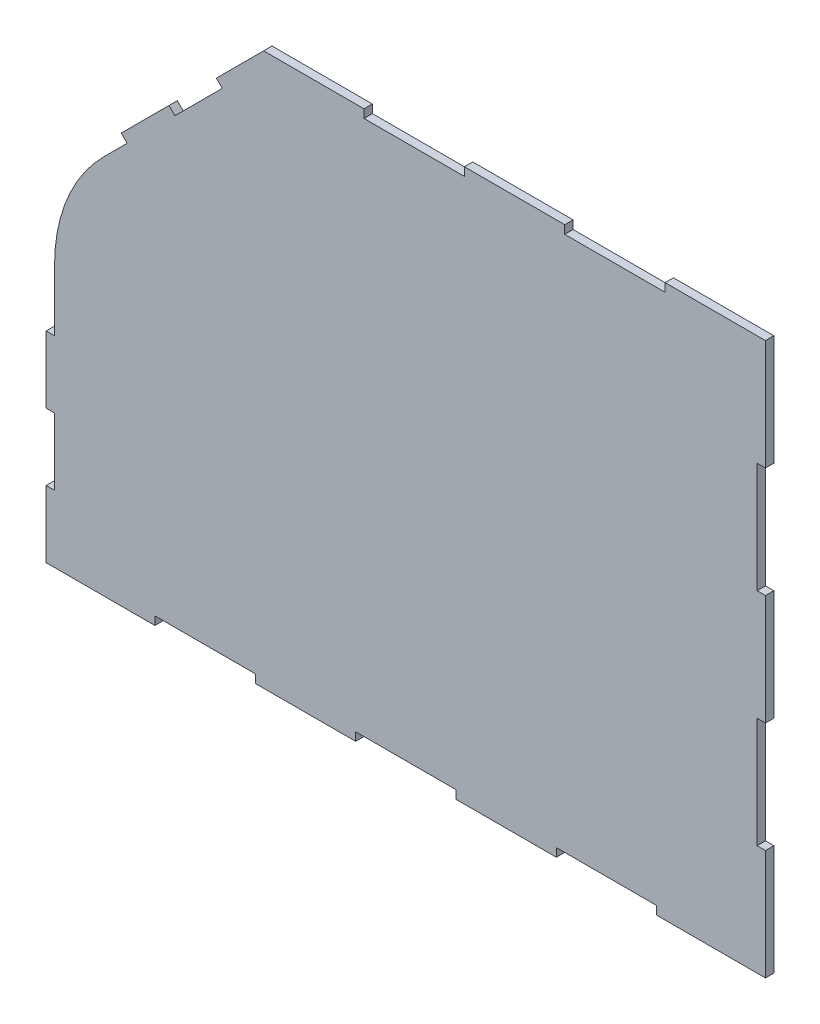
SolidWorks part; units mm, degrees
material "Contreplaqué pin"
ref_plane "Plan de face" through (0, 0, 0) normal (0, 0, 1) x (1, 0, 0)
ref_plane "Plan de dessus" through (0, 0, 0) normal (0, 1, 0) x (1, 0, 0)
ref_plane "Plan de droite" through (0, 0, 0) normal (1, 0, 0) x (0, 0, -1)
sketch "Esquisse1" plane through (0, 0, 0) normal (0, 0, 1) x (1, 0, 0)
  line L1 (0, 330) -> (-60, 330)
  line L2 (-300, 330) -> (-328.2843, 301.7157)
  line L3 (-430, 200) -> (-430, 160)
  line L4 (-305, 0) -> (-245, 0)
  line L5 (-240, 330) -> (-300, 330)
  line L7 (-240, 330) -> (-240, 325)
  line L8 (-240, 325) -> (-180, 325)
  line L9 (-180, 330) -> (-180, 325)
  line L11 (-120, 330) -> (-120, 325)
  line L12 (-120, 325) -> (-60, 325)
  line L13 (-60, 330) -> (-60, 325)
  line L14 (-120, 330) -> (-180, 330)
  line L31 (-328.2843, 301.7157) -> (-324.7487, 298.1802)
  line L32 (-324.7487, 298.1802) -> (-353.033, 269.8959)
  line L33 (-353.033, 269.8959) -> (-356.5685, 273.4315)
  line L34 (-399.9019, 230.0981) -> (-396.3663, 226.5626)
  line L35 (-396.3663, 226.5626) -> (-411.4154, 211.5135)
  line L36 (-411.4154, 211.5135) -> (-414.9509, 215.0491)
  line L37 (-356.5685, 273.4315) -> (-399.9019, 230.0981)
  line L38 (-414.9509, 215.0491) -> (-430, 200)
  line L39 (-430, 120) -> (-430, 80)
  line L44 (-430, 160) -> (-425, 160)
  line L46 (-430, 120) -> (-425, 120)
  line L47 (-425, 160) -> (-425, 120)
  line L48 (-430, 80) -> (-425, 80)
  line L50 (-430, 40) -> (-425, 40)
  line L51 (-425, 80) -> (-425, 40)
  line L52 (-430, 40) -> (-430, 0)
  line L53 (0, 0) -> (0, 66)
  line L54 (0, 66) -> (-5, 66)
  line L55 (-5, 66) -> (-5, 132)
  line L56 (-5, 132) -> (0, 132)
  line L57 (0, 132) -> (0, 198)
  line L58 (0, 198) -> (-5, 198)
  line L59 (-5, 198) -> (-5, 264)
  line L60 (-5, 264) -> (0, 264)
  line L61 (0, 264) -> (0, 330)
  line L62 (-384.8528, 245.1472) -> (-351.7904, 212.0848) construction
  line L63 (-365, 0) -> (-365, 5)
  line L64 (-365, 5) -> (-305, 5)
  line L65 (-305, 5) -> (-305, 0)
  line L66 (-305, 0) -> (-245, 0)
  line L67 (-245, 0) -> (-245, 5)
  line L68 (-245, 5) -> (-185, 5)
  line L69 (-185, 5) -> (-185, 0)
  line L70 (-185, 0) -> (-125, 0)
  line L71 (-125, 0) -> (-125, 5)
  line L72 (-125, 5) -> (-65, 5)
  line L73 (-65, 5) -> (-65, 0)
  line L74 (-65, 0) -> (0, 0)
  line L75 (-430, 0) -> (-365, 0)
  line L76 (-185, 0) -> (-125, 0)
  line L77 (-65, 0) -> (0, 0)
  point P42 (-430, 180)
  dimension "D1" = 200
  dimension "D2" = 330
  dimension "D3" = 300
  dimension "D5" = 5
  dimension "D8" = 5
  dimension "D9" = 5
  dimension "D4" = 430
  dimension "D6" = 5
  dimension "D7" = 120
  dimension "D10" = 63.8478
  dimension "D11" = 40
  dimension "D12" = 40
  dimension "D13" = 21.2826
  dimension "D14" = 21.2826
  dimension "D15" = 65
  dimension "D16" = 65
  dimension "D17" = 60
  dimension "D18" = 5
extrude "Boss.-Extru.1" add sketch "Esquisse1" along normal blind 5
sketch "Esquisse2" plane through (0, 0, 5) normal (0, 0, 1) x (1, 0, 0)
  line L0 (-395.7107, 227.2183) -> (-381.5685, 241.3604)
  line L1 (-381.5685, 241.3604) -> (-385.1041, 244.8959)
  line L2 (-425, 156.5076) -> (-430, 156.5076)
  line L3 (-430, 156.5076) -> (-430, 200)
  line L4 (-430, 200) -> (-385.1041, 244.8959)
  line L5 (-356.5685, 273.4315) -> (-399.9019, 230.0981) construction
  line L9 (-430, 120) -> (-430, 80) construction
  line L10 (-324.7487, 298.1802) -> (-353.033, 269.8959) construction
  line L11 (-425, 160) -> (-425, 120) construction
  arc A0 (-395.7107, 227.2183) -> (-425, 156.5076) centre (-325, 156.5076) ccw
  dimension "D1" = 100
  dimension "D3" = 20
extrude "Enlèv. mat.-Extru.1" cut sketch "Esquisse2" against normal up to next
sketch "Esquisse3" [suppressed] plane through (0, 0, 5) normal (0, 0, 1) x (1, 0, 0)
  line L1 (-185, 200) -> (-195, 200)
  line L2 (-180, 195) -> (-180, 165)
  line L3 (-185, 160) -> (-195, 160)
  line L4 (-200, 195) -> (-200, 165)
  line L6 (0, 0) -> (0, 66) construction
  line L7 (-305, 0) -> (-245, 0) construction
  arc A0 (-180, 195) -> (-185, 200) centre (-185, 195) ccw
  arc A1 (-185, 160) -> (-180, 165) centre (-185, 165) ccw
  arc A2 (-200, 165) -> (-195, 160) centre (-195, 165) ccw
  arc A3 (-200, 195) -> (-195, 200) centre (-195, 195) cw
  point P10 (-180, 200)
  point P13 (-180, 160)
  dimension "D5" = 5
  dimension "D1" = 200
  dimension "D2" = 160
  dimension "D3" = 40
  dimension "D4" = 20
extrude "Enlèv. mat.-Extru.2" [suppressed] cut sketch "Esquisse3" against normal up to next
equation "\"D11@Esquisse1\"=\"D7@Esquisse1\"/3"
equation "\"D12@Esquisse1\"=\"D11@Esquisse1\""
equation "\"D13@Esquisse1\"=\"D10@Esquisse1\"/3"
equation "\"D14@Esquisse1\"=\"D13@Esquisse1\""
